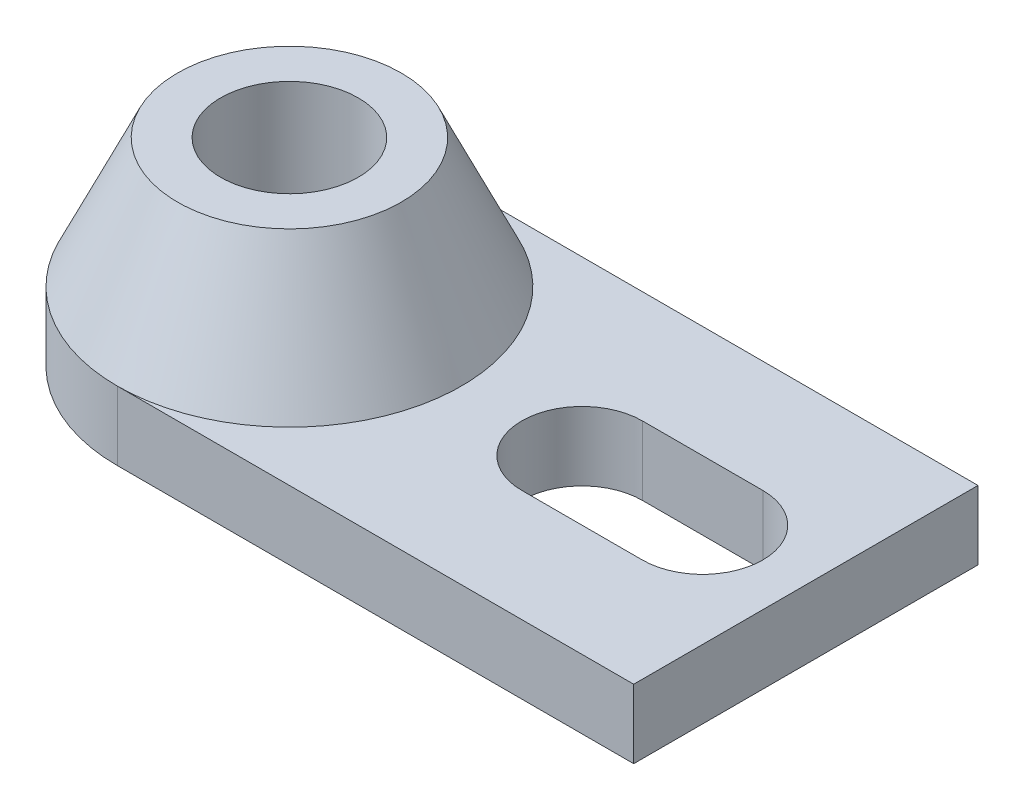
SolidWorks part; units mm, degrees
material "Cast Alloy Steel"
ref_plane "Front Plane" through (0, 0, 0) normal (0, 0, 1) x (1, 0, 0)
ref_plane "Top Plane" through (0, 0, 0) normal (0, 1, 0) x (1, 0, 0)
ref_plane "Right Plane" through (0, 0, 0) normal (1, 0, 0) x (0, 0, -1)
sketch "Sketch2" plane through (0, 0, 0) normal (0, 1, 0) x (1, 0, 0)
  line L1 (0, -20) -> (-60, -20)
  line L2 (0, -20) -> (0, 20)
  line L3 (0, 20) -> (-60, 20)
  line L5 (-26, 7) -> (-12, 7)
  line L7 (-26, -7) -> (-12, -7)
  line L9 (-26, 7) -> (-12, -7) construction
  line L10 (-26, -7) -> (-12, 7) construction
  arc A0 (-60, -20) -> (-60, 20) centre (-60, 0) cw
  arc A1 (-26, -7) -> (-26, 7) centre (-26, 0) cw
  arc A2 (-12, -7) -> (-12, 7) centre (-12, 0) ccw
  point P4 (-19, 0)
  dimension "D1" = 40
  dimension "D2" = 60
  dimension "D3" = 14
  dimension "D4" = 14
  dimension "D5" = 12
extrude "Boss-Extrude2" add sketch "Sketch2" along normal blind 8
sketch "Sketch4" plane through (0, 0, 0) normal (0, 0, 1) x (1, 0, 0)
  line L0 (-68, 8) -> (-68, 23)
  line L1 (-60, 8) -> (-80, 8) construction
  line L2 (-68, 23) -> (-73, 23)
  line L3 (-73, 23) -> (-80, 8)
  line L4 (-80, 8) -> (-68, 8)
  line L5 (-60, 8) -> (-60, 30.0019) construction
  dimension "D1" = 5
  dimension "D2" = 15
  dimension "D3" = 8
revolve "Revolve4" add sketch "Sketch4" angle 360 about L5
